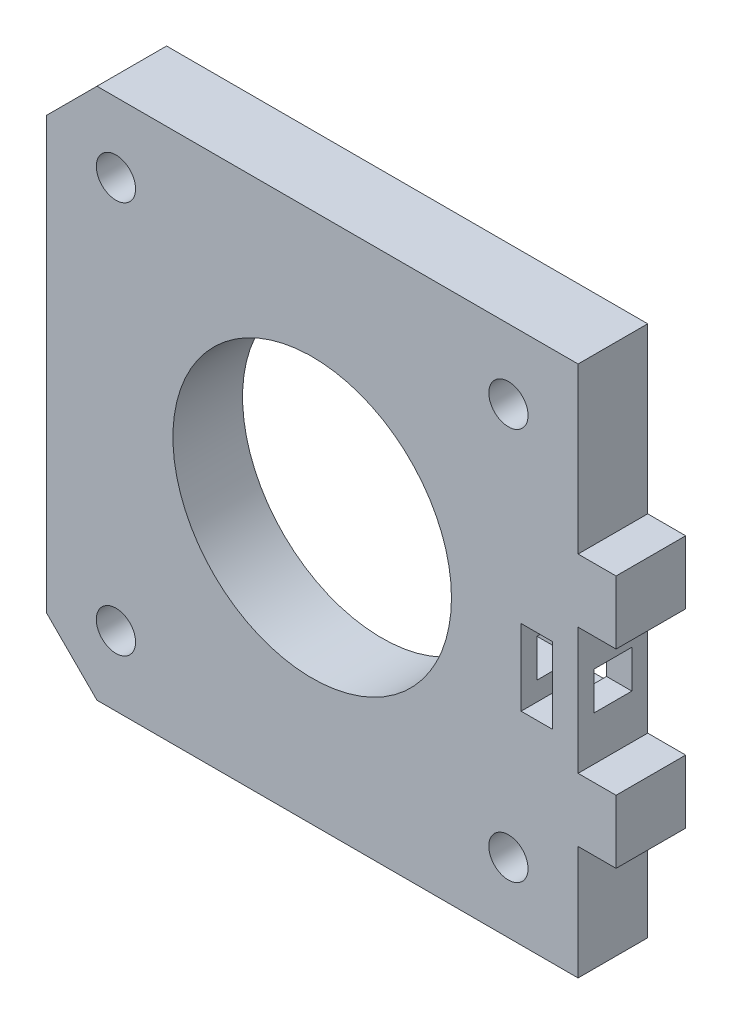
SolidWorks part; units mm, degrees
ref_plane "Alzado" through (0, 0, 0) normal (0, 0, 1) x (1, 0, 0)
ref_plane "Planta" through (0, 0, 0) normal (0, 1, 0) x (1, 0, 0)
ref_plane "Vista lateral" through (0, 0, 0) normal (1, 0, 0) x (0, 0, -1)
sketch "Croquis1" plane through (0, 0, 0) normal (0, 0, 1) x (1, 0, 0)
  line L0 (0, 4) -> (0, 38)
  line L1 (4, 42) -> (42, 42)
  line L2 (42, 42) -> (42, 0)
  line L3 (42, 0) -> (4, 0)
  line L4 (0, 0) -> (0.3166, 0.4221)
  line L5 (0, 38) -> (4, 42)
  line L6 (4, 0) -> (0, 4)
  circle A0 centre (5.5, 36.5) radius 1.55
  circle A1 centre (5.5, 5.5) radius 1.55
  circle A2 centre (36.5, 5.5) radius 1.55
  circle A3 centre (36.5, 36.5) radius 1.55
  circle A4 centre (21, 21) radius 11
  point P1 (0, 42)
  dimension "D3" = 3.1
  dimension "D4" = 3.1
  dimension "D5" = 3.1
  dimension "D6" = 3.1
  dimension "D13" = 22
  dimension "D1" = 42
  dimension "D2" = 42
  dimension "D7" = 31
  dimension "D10" = 31
  dimension "D11" = 5.5
  dimension "D12" = 5.5
  dimension "D14" = 21
  dimension "D15" = 21
extrude "Saliente-Extruir1" add sketch "Croquis1" along normal blind 5.5 contours L6 L3 L2 L1 L5 L0 A4 A3 A2 A1 A0
sketch "Croquis3" plane through (42, 0, 0) normal (1, 0, 0) x (0, 0, -1)
  line L0 (-5.5, 29) -> (0, 29)
  line L1 (-5.5, 42) -> (-5.5, 0) construction
  line L2 (0, 42) -> (0, 0) construction
  line L3 (0, 29) -> (0, 24)
  line L4 (0, 24) -> (-5.5, 24)
  line L5 (-5.5, 24) -> (-5.5, 29)
  line L6 (-5.5, 42) -> (0, 42) construction
  line L7 (-5.5, 14) -> (0, 14)
  line L8 (0, 14) -> (0, 9)
  line L9 (0, 9) -> (-5.5, 9)
  line L10 (-5.5, 9) -> (-5.5, 14)
  dimension "D1" = 5
  dimension "D2" = 13
  dimension "D3" = 5
  dimension "D4" = 10
extrude "Saliente-Extruir3" add sketch "Croquis3" along normal blind 3
sketch "Croquis6" plane through (42, 0, 0) normal (1, 0, 0) x (0, 0, -1)
  line L0 (-5.5, 24) -> (0, 24) construction
  line L1 (-4.25, 20.5) -> (-1.25, 20.5)
  line L2 (-4.25, 20.5) -> (-4.25, 17.5)
  line L3 (-4.25, 17.5) -> (-1.25, 17.5)
  line L4 (-1.25, 20.5) -> (-1.25, 17.5)
  line L5 (-4.25, 20.5) -> (-1.25, 17.5) construction
  line L6 (-4.25, 17.5) -> (-1.25, 20.5) construction
  line L8 (-5.5, 24) -> (-5.5, 14) construction
  point P0 (-2.75, 19)
  dimension "D1" = 3
  dimension "D2" = 3
  dimension "D3" = 5
  dimension "D4" = 2.75
extrude "Cortar-Extruir2" cut sketch "Croquis6" against normal blind 8
sketch "Croquis7" plane through (0, 0, 5.5) normal (0, 0, 1) x (1, 0, 0)
  line L0 (37.5, 22) -> (40, 22)
  line L1 (40, 22) -> (40, 16)
  line L2 (40, 16) -> (37.5, 16)
  line L3 (37.5, 16) -> (37.5, 22)
  line L4 (42, 24) -> (42, 14) construction
  line L5 (42, 24) -> (42, 14)
  point P6 (42, 19)
  point P7 (40, 19)
  dimension "D1" = 2.5
  dimension "D2" = 6
  dimension "D3" = 2
extrude "Cortar-Extruir3" cut sketch "Croquis7" against normal through all contours L3 L2 L1 L0
